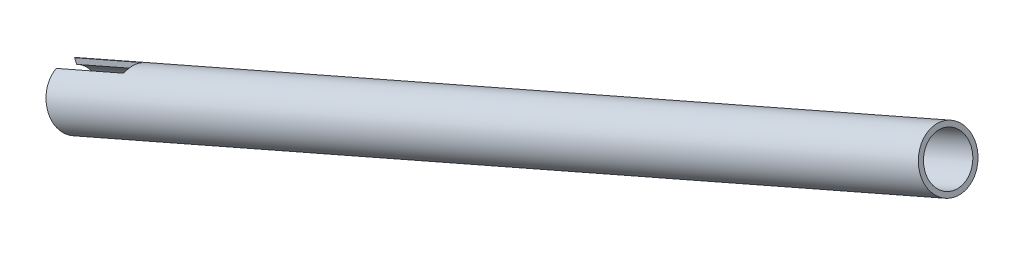
SolidWorks part; units mm, degrees
ref_plane "Front" through (0, 0, 0) normal (0, 0, 1) x (1, 0, 0)
ref_plane "Top" through (0, 0, 0) normal (0, 1, 0) x (1, 0, 0)
ref_plane "Right" through (0, 0, 0) normal (1, 0, 0) x (0, 0, -1)
sketch "Sketch1" plane through (0, 0, 0) normal (0, 0, 1) x (1, 0, 0)
  line L0 (-487.6846, 44.5022) -> (-529.9355, 25.9995) construction
  line L1 (-609.6, -8.8876) -> (-241.3, 152.4) construction
  line L2 (-283.2207, 125.4459) -> (-583.1746, -5.9112)
  line L3 (-583.1746, -5.9112) -> (-582.5123, -7.4235)
  line L4 (-582.5123, -7.4235) -> (-282.5585, 123.9336)
  line L5 (-282.5585, 123.9336) -> (-283.2207, 125.4459)
  dimension "D1" = 1.651
  dimension "D2" = 9.525
revolve "Revolve1" add sketch "Sketch1" angle 360 about L0
sketch "Sketch2" plane through (0, 0, 0) normal (0, 0, 1) x (1, 0, 0)
  line L0 (-566.8874, 20.2156) -> (-590.1541, 10.0265)
  line L1 (-590.1541, 10.0265) -> (-582.5123, -7.4235)
  line L2 (-582.5123, -7.4235) -> (-559.2456, 2.7656)
  line L3 (-559.2456, 2.7656) -> (-566.8874, 20.2156)
  line L5 (-290.2003, 141.3837) -> (-590.1541, 10.0265) construction
  line L6 (-582.5123, -7.4235) -> (-282.5585, 123.9336) construction
  line L8 (-590.1541, 10.0265) -> (-582.5123, -7.4235) construction
  line L9 (-560.8249, 6.3719) -> (-558.2776, 0.5552) construction
extrude "Cut-Extrude1" cut sketch "Sketch2" against normal up to surface and the other way up to surface
move or copy body "Body-Move/Copy1" [suppressed] bodies to move or copy 102
equation "\"D1@Sketch1\"=\"a arm tube thickness@FS2-SU-RS-A-0002-V1, REAR LEFT SUSPENSION-1.Assembly@FS2-SU-RS-A-0001-V1, REAR SUSPENSION-1.Assembly\""
equation "\"D2@Sketch1\"=\"a arm tube diameter@FS2-SU-RS-A-0002-V1, REAR LEFT SUSPENSION-1.Assembly@FS2-SU-RS-A-0001-V1, REAR SUSPENSION-1.Assembly\"/2"
